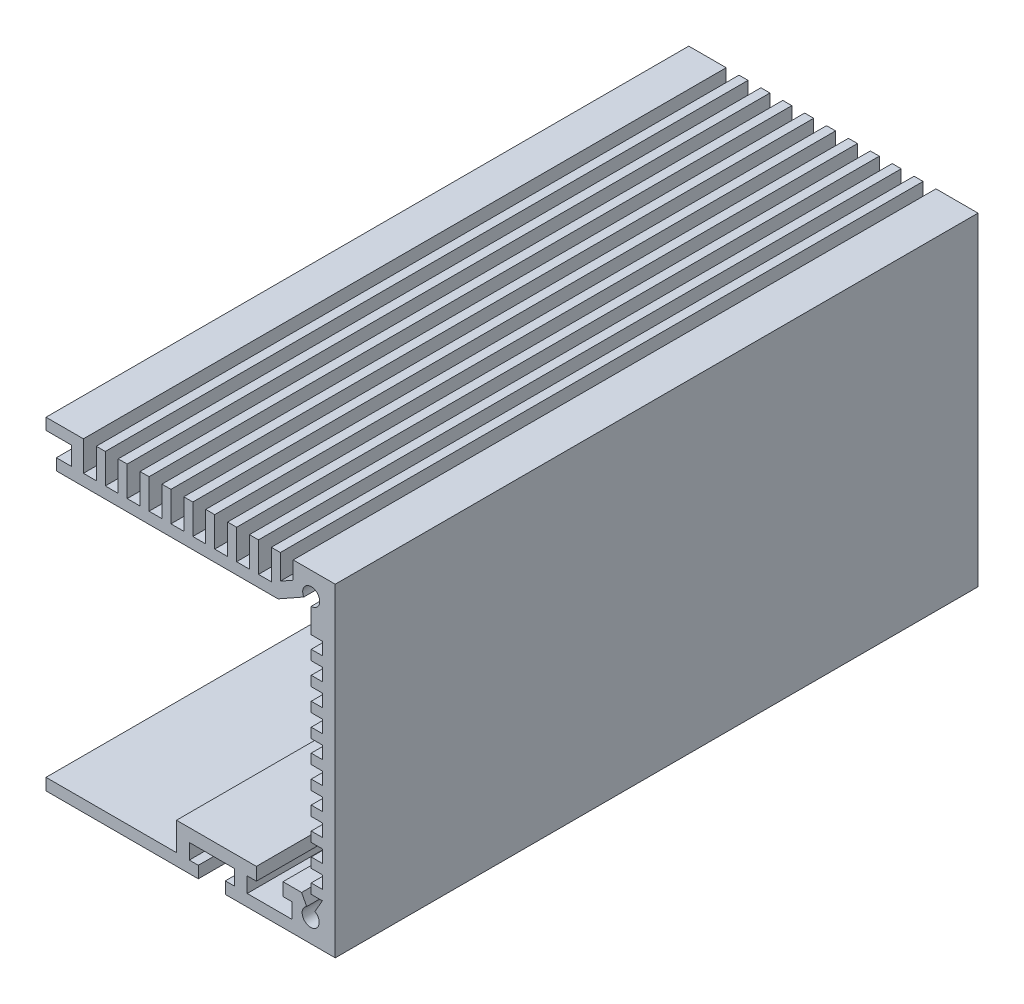
SolidWorks part; units mm, degrees
ref_plane "Front Plane" through (0, 0, 0) normal (0, 0, 1) x (1, 0, 0)
ref_plane "Top Plane" through (0, 0, 0) normal (0, 1, 0) x (1, 0, 0)
ref_plane "Right Plane" through (0, 0, 0) normal (1, 0, 0) x (0, 0, -1)
sketch "Sketch2" plane through (0, 0, 0) normal (0, 0, -1) x (-1, 0, 0)
  line L0 (-90, 0) -> (-90, 50.35) construction
  line L1 (-81.1, 43.92) -> (-46.615, 43.92)
  line L2 (-88, 11.7275) -> (-88, 13.6875)
  line L3 (-83.3, 1.83) -> (-76.3, 1.83)
  line L4 (-50.82, 50.35) -> (-45, 50.35)
  line L5 (-45, 50.35) -> (-45, 0) construction
  line L6 (-90, 50.35) -> (0, 50.35) construction
  line L7 (0, 0) -> (-90, 0) construction
  line L8 (-77.73, 4.2) -> (-76.3, 4.2)
  line L9 (-65.3, 1.83) -> (-65.3, 6.2)
  line L10 (-65.3, 6.2) -> (-77.73, 6.2)
  line L11 (-77.73, 4.2) -> (-77.73, 6.2)
  line L12 (-76.3, 4.2) -> (-76.3, 1.83)
  line L13 (-72.9, 1.83) -> (-72.9, 0)
  line L14 (-74.3, 4.2) -> (-67.3, 4.2)
  line L15 (-74.3, 4.2) -> (-74.3, 1.83)
  line L16 (-74.3, 1.83) -> (-72.9, 1.83)
  line L17 (-67.3, 4.2) -> (-67.3, 1.83)
  line L18 (-72.9, 0) -> (-90, 0)
  line L19 (-68.7, 0) -> (-68.7, 1.83)
  line L20 (-68.7, 1.83) -> (-67.3, 1.83)
  line L21 (-83.3, 1.83) -> (-83.3, 4.2)
  line L22 (-83.3, 4.2) -> (-81.87, 4.2)
  line L23 (-81.87, 4.2) -> (-81.87, 6.2)
  line L24 (-81.87, 6.2) -> (-84.7656, 6.2)
  line L25 (-88, 8.23) -> (-88, 10.19)
  line L26 (-88, 6.6925) -> (-86.8365, 4.6731)
  line L27 (-88, 8.23) -> (-86.26, 8.23)
  line L28 (-86.26, 6.6925) -> (-88, 6.6925)
  line L29 (-88, 11.7275) -> (-86.26, 11.7275)
  line L30 (-86.26, 8.23) -> (-86.26, 6.6925)
  line L31 (-86.26, 11.7275) -> (-86.26, 10.19)
  line L32 (-86.26, 10.19) -> (-88, 10.19)
  line L33 (-85.5574, 4.6972) -> (-84.7656, 6.2)
  line L34 (-88, 15.225) -> (-88, 17.185)
  line L35 (-88, 15.225) -> (-86.26, 15.225)
  line L36 (-86.26, 15.225) -> (-86.26, 13.6875)
  line L37 (-86.26, 13.6875) -> (-88, 13.6875)
  line L38 (-88, 18.7225) -> (-88, 20.6825)
  line L39 (-88, 18.7225) -> (-86.26, 18.7225)
  line L40 (-86.26, 18.7225) -> (-86.26, 17.185)
  line L41 (-86.26, 17.185) -> (-88, 17.185)
  line L42 (-88, 22.22) -> (-88, 24.18)
  line L43 (-88, 22.22) -> (-86.26, 22.22)
  line L44 (-86.26, 22.22) -> (-86.26, 20.6825)
  line L45 (-86.26, 20.6825) -> (-88, 20.6825)
  line L46 (-88, 25.7175) -> (-88, 27.6775)
  line L47 (-88, 25.7175) -> (-86.26, 25.7175)
  line L48 (-86.26, 25.7175) -> (-86.26, 24.18)
  line L49 (-86.26, 24.18) -> (-88, 24.18)
  line L50 (-88, 29.215) -> (-88, 31.175)
  line L51 (-88, 29.215) -> (-86.26, 29.215)
  line L52 (-86.26, 29.215) -> (-86.26, 27.6775)
  line L53 (-86.26, 27.6775) -> (-88, 27.6775)
  line L54 (-88, 32.7125) -> (-88, 34.6725)
  line L55 (-88, 32.7125) -> (-86.26, 32.7125)
  line L56 (-86.26, 32.7125) -> (-86.26, 31.175)
  line L57 (-86.26, 31.175) -> (-88, 31.175)
  line L58 (-88, 36.21) -> (-88, 38.17)
  line L59 (-88, 36.21) -> (-86.26, 36.21)
  line L60 (-86.26, 36.21) -> (-86.26, 34.6725)
  line L61 (-86.26, 34.6725) -> (-88, 34.6725)
  line L62 (-88, 39.7075) -> (-88, 41.6675)
  line L63 (-88, 39.7075) -> (-86.26, 39.7075)
  line L64 (-86.26, 39.7075) -> (-86.26, 38.17)
  line L65 (-86.26, 38.17) -> (-88, 38.17)
  line L66 (-88, 8.23) -> (-88, 11.7275) construction
  line L67 (-88, 41.6675) -> (-86.26, 41.6675)
  line L68 (-86.26, 41.6675) -> (-86.26, 45.5)
  line L69 (-85.1054, 46.175) -> (-81.1, 43.92)
  line L70 (-46.615, 43.92) -> (-46.615, 45.7)
  line L71 (-46.615, 45.7) -> (-49, 45.7)
  line L72 (-49, 45.7) -> (-49, 48.57)
  line L73 (-45, 50.35) -> (-45, 48.57)
  line L74 (-45, 48.57) -> (-49, 48.57)
  line L75 (-68.7, 0) -> (-45, 0)
  line L76 (-50.82, 50.35) -> (-50.82, 45.7)
  line L77 (-50.82, 45.7) -> (-52.82, 45.7)
  line L78 (-52.82, 50.35) -> (-52.82, 45.7)
  line L79 (-56.2244, 50.35) -> (-56.2244, 45.7)
  line L80 (-54.2244, 50.35) -> (-54.2244, 45.7)
  line L81 (-54.2244, 45.7) -> (-56.2244, 45.7)
  line L82 (-45, 0) -> (-45, 1.83)
  line L83 (-59.6289, 50.35) -> (-59.6289, 45.7)
  line L84 (-57.6289, 50.35) -> (-57.6289, 45.7)
  line L85 (-57.6289, 45.7) -> (-59.6289, 45.7)
  line L86 (-45, 1.83) -> (-65.3, 1.83)
  line L87 (-63.0333, 50.35) -> (-63.0333, 45.7)
  line L88 (-61.0333, 50.35) -> (-61.0333, 45.7)
  line L89 (-61.0333, 45.7) -> (-63.0333, 45.7)
  line L91 (-66.4378, 50.35) -> (-66.4378, 45.7)
  line L92 (-64.4378, 50.35) -> (-64.4378, 45.7)
  line L93 (-64.4378, 45.7) -> (-66.4378, 45.7)
  line L95 (-69.8422, 50.35) -> (-69.8422, 45.7)
  line L96 (-67.8422, 50.35) -> (-67.8422, 45.7)
  line L97 (-67.8422, 45.7) -> (-69.8422, 45.7)
  line L99 (-73.2467, 50.35) -> (-73.2467, 45.7)
  line L100 (-71.2467, 50.35) -> (-71.2467, 45.7)
  line L101 (-71.2467, 45.7) -> (-73.2467, 45.7)
  line L103 (-76.6511, 50.35) -> (-76.6511, 45.7)
  line L104 (-74.6511, 50.35) -> (-74.6511, 45.7)
  line L105 (-74.6511, 45.7) -> (-76.6511, 45.7)
  line L107 (-80.0556, 50.35) -> (-80.0556, 45.7)
  line L108 (-78.0556, 50.35) -> (-78.0556, 45.7)
  line L109 (-78.0556, 45.7) -> (-80.0556, 45.7)
  line L111 (-83.46, 50.35) -> (-83.46, 47.6166)
  line L112 (-81.46, 50.35) -> (-81.46, 46.4907)
  line L114 (-83.46, 47.6166) -> (-81.46, 46.4907)
  line L116 (-81.46, 45.7) -> (-83.46, 45.7) [skipped]
  line L223 (-81.46, 50.35) -> (-80.0556, 50.35)
  line L224 (-90, 50.35) -> (-83.46, 50.35)
  line L225 (-90, 50.35) -> (-90, 0)
  line L230 (-78.0556, 50.35) -> (-76.6511, 50.35)
  line L232 (-74.6511, 50.35) -> (-73.2467, 50.35)
  line L234 (-71.2467, 50.35) -> (-69.8422, 50.35)
  line L236 (-67.8422, 50.35) -> (-66.4378, 50.35)
  line L238 (-64.4378, 50.35) -> (-63.0333, 50.35)
  line L240 (-61.0333, 50.35) -> (-59.6289, 50.35)
  line L242 (-57.6289, 50.35) -> (-56.2244, 50.35)
  line L244 (-54.2244, 50.35) -> (-52.82, 50.35)
  arc A0 (-86.8365, 4.6731) -> (-85.5574, 4.6972) centre (-86.175, 3.525) ccw
  arc A1 (-85.1054, 46.175) -> (-86.26, 45.5) centre (-86.26, 46.825) ccw
  point P34 (-86.175, 2.2)
  point P35 (-87.5, 3.525)
  point P56 (-87.585, 46.825)
  point P61 (-86.26, 48.15)
  point P179 (-45, 48.57)
  point P242 (-45, 1.83)
  dimension "D12" = 2.65
  dimension "D2" = 6.43
  dimension "D3" = 1.83
  dimension "D4" = 24.7
  dimension "D5" = 6.2
  dimension "D6" = 12.43
  dimension "D7" = 2
  dimension "D8" = 2
  dimension "D9" = 2
  dimension "D10" = 4.2
  dimension "D11" = 7
  dimension "D13" = 2.2
  dimension "D14" = 2.5
  dimension "D15" = 3.6874
  dimension "D16" = 8.23
  dimension "D17" = 12.18
  dimension "D18" = 2
  dimension "D19" = 1.96
  dimension "D20" = 3.74
  dimension "D22" = 2.2
  dimension "D23" = 8.9
  dimension "D25" = 1.78
  dimension "D26" = 41
  dimension "3.25/2" = 1.615
  dimension "D27" = 1.82
  dimension "D28" = 2
  dimension "D30" = 6.54
  dimension "D21" = 10
  dimension "D29" = 10
extrude "Boss-Extrude1" add sketch "Sketch2" along normal blind 100
